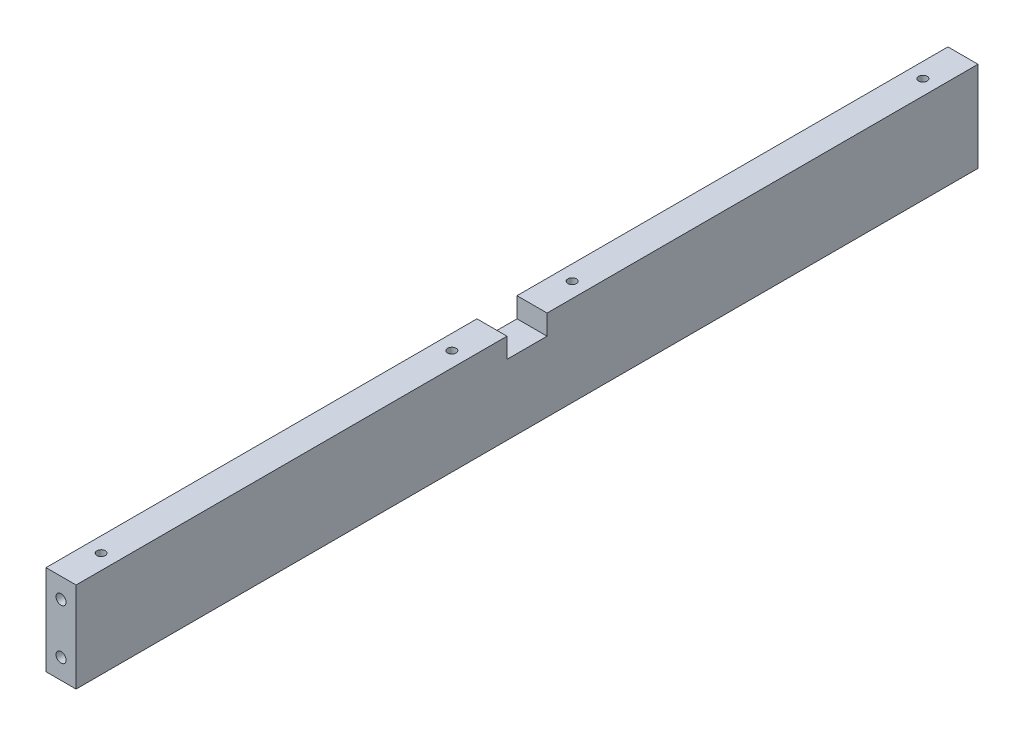
SolidWorks part; units mm, degrees
ref_plane "Plan de face" through (0, 0, 0) normal (0, 0, 1) x (1, 0, 0)
ref_plane "Plan de dessus" through (0, 0, 0) normal (0, 1, 0) x (1, 0, 0)
ref_plane "Plan de droite" through (0, 0, 0) normal (1, 0, 0) x (0, 0, -1)
sketch "Esquisse1" plane through (0, 0, 0) normal (0, 0, 1) x (1, 0, 0)
  line L1 (0, 0) -> (-15, 0)
  line L2 (0, 0) -> (0, 45)
  line L3 (0, 45) -> (-15, 45)
  line L4 (-15, 0) -> (-15, 45)
  dimension "D1" = 15
  dimension "D2" = 45
extrude "Boss.-Extru.1" add sketch "Esquisse1" along normal blind 450
hole_wizard "Trou pour taraudage pour trou taraudé M61" positions "Esquisse7" profile "Esquisse6" hole size "M6" standard "ISO"
sketch "Esquisse7" plane through (0, 0, 450) normal (0, 0, 1) x (1, 0, 0)
  line L0 (0, 45) -> (-15, 45) construction
  line L1 (-15, 0) -> (0, 0) construction
  line L2 (0, 0) -> (0, 45) construction
  line L3 (-15, 45) -> (-15, 0) construction
  point P0 (-7.5, 35)
  point P2 (-7.5, 10)
  dimension "D1" = 10
  dimension "D2" = 10
  dimension "D3" = 7.5
  dimension "D4" = 7.5
sketch "Esquisse6" plane through (-7.5, 35, 450) normal (1, 0, 0) x (0, -1, 0)
  line L0 (0, 0) -> (0, 11.5022)
  line L1 (0, 11.5022) -> (2.5, 10)
  line L2 (2.5, 10) -> (2.5, 0)
  line L5 (2.5, 0) -> (0, 0)
  line L10 (0, 11.5022) -> (-2.5, 10) construction
  line L11 (0, -6.35) -> (0, 107.95) construction
  dimension "Diamètre du perçage" = 5
  dimension "Profondeur du perçage" = 10
  dimension "Angle de pointe" = 118
hole_wizard "Trou pour taraudage pour trou taraudé M62" positions "Esquisse9" profile "Esquisse8" hole size "M6" standard "ISO"
sketch "Esquisse9" plane through (0, 0, 0) normal (0, 0, -1) x (-1, 0, 0)
  line L0 (0, 45) -> (15, 45) construction
  line L1 (15, 0) -> (0, 0) construction
  line L2 (15, 45) -> (15, 0) construction
  line L3 (0, 0) -> (0, 45) construction
  point P0 (7.5, 35)
  point P2 (7.5, 10)
  dimension "D1" = 10
  dimension "D2" = 10
  dimension "D3" = 7.5
  dimension "D4" = 7.5
sketch "Esquisse8" plane through (-7.5, 35, 0) normal (1, 0, 0) x (0, 1, 0)
  line L0 (0, 0) -> (0, 11.5022)
  line L1 (0, 11.5022) -> (2.5, 10)
  line L2 (2.5, 10) -> (2.5, 0)
  line L5 (2.5, 0) -> (0, 0)
  line L10 (0, 11.5022) -> (-2.5, 10) construction
  line L11 (0, -6.35) -> (0, 107.95) construction
  dimension "Diamètre du perçage" = 5
  dimension "Profondeur du perçage" = 10
  dimension "Angle de pointe" = 118
sketch "Esquisse10" plane through (0, 0, 0) normal (1, 0, 0) x (0, 0, -1)
  line L0 (-450, 45) -> (0, 45) construction
  line L1 (-235, 45) -> (-215, 45)
  line L2 (-235, 45) -> (-235, 35)
  line L3 (-235, 35) -> (-215, 35)
  line L4 (-215, 45) -> (-215, 35)
  line L5 (0, 0) -> (0, 45) construction
  dimension "D1" = 20
  dimension "D2" = 10
  dimension "D3" = 215
extrude "Enlèv. mat.-Extru.1" cut sketch "Esquisse10" against normal blind 15
hole_wizard "Trou pour taraudage pour trou taraudé M51" positions "Esquisse12" profile "Esquisse11" hole size "M5" standard "ISO"
sketch "Esquisse12" plane through (0, 45, 0) normal (0, 1, 0) x (1, 0, 0)
  line L0 (0, -450) -> (-15, -450) construction
  line L1 (-15, -235) -> (0, -235) construction
  line L2 (-15, -215) -> (0, -215) construction
  line L3 (0, 0) -> (-15, 0) construction
  line L4 (0, -215) -> (0, 0) construction
  line L5 (0, -450) -> (0, -235) construction
  point P0 (-7.5, -430)
  point P2 (-7.5, -255)
  point P4 (-7.5, -195)
  point P6 (-7.5, -20)
  point P13 (-7.5, -215)
  point P16 (-7.5, 0)
  dimension "D1" = 20
  dimension "D2" = 20
  dimension "D3" = 20
  dimension "D4" = 20
  dimension "D5" = 7.5
  dimension "D6" = 7.5
  dimension "D7" = 7.5
  dimension "D8" = 7.5
sketch "Esquisse11" plane through (-7.5, 45, 430) normal (1, 0, 0) x (0, 0, 1)
  line L0 (0, 0) -> (0, 26.2618)
  line L1 (0, 26.2618) -> (2.1, 25)
  line L2 (2.1, 25) -> (2.1, 0)
  line L5 (2.1, 0) -> (0, 0)
  line L10 (0, 26.2618) -> (-2.1, 25) construction
  line L11 (0, -6.35) -> (0, 107.95) construction
  dimension "Diamètre du perçage" = 4.2
  dimension "Profondeur du perçage" = 25
  dimension "Angle de pointe" = 118
